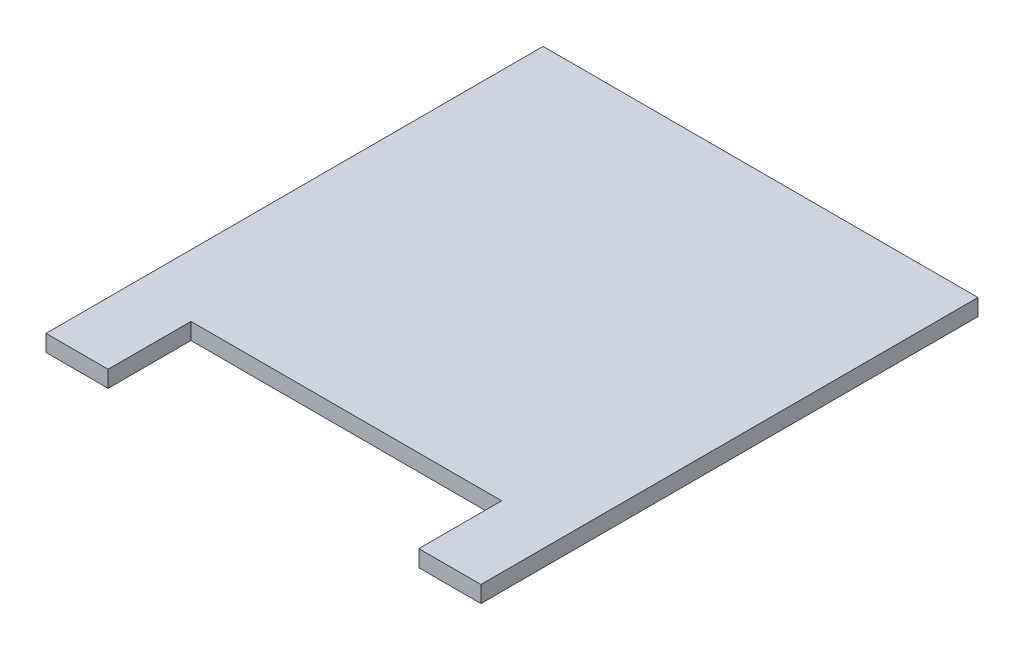
SolidWorks part; units mm, degrees
ref_plane "Alzado" through (0, 0, 0) normal (0, 0, 1) x (1, 0, 0)
ref_plane "Planta" through (0, 0, 0) normal (0, 1, 0) x (1, 0, 0)
ref_plane "Vista lateral" through (0, 0, 0) normal (1, 0, 0) x (0, 0, -1)
sketch "Croquis1" plane through (0, 0, 0) normal (0, 1, 0) x (1, 0, 0)
  line L0 (150, -240) -> (210, -240)
  line L1 (-210, -240) -> (-150, -240)
  line L2 (-210, -240) -> (-210, 240)
  line L3 (-210, 240) -> (210, 240)
  line L4 (210, -240) -> (210, 240)
  line L5 (-210, -240) -> (210, 240) construction
  line L6 (-210, 240) -> (210, -240) construction
  line L8 (-150, -240) -> (-150, -160)
  line L9 (-150, -160) -> (150, -160)
  line L10 (150, -240) -> (150, -160)
  point P0 (0, 0)
  dimension "D1" = 480
  dimension "D2" = 420
  dimension "D3" = 60
  dimension "D4" = 300
  dimension "D5" = 80
extrude "Saliente-Extruir1" add sketch "Croquis1" along normal blind 16
